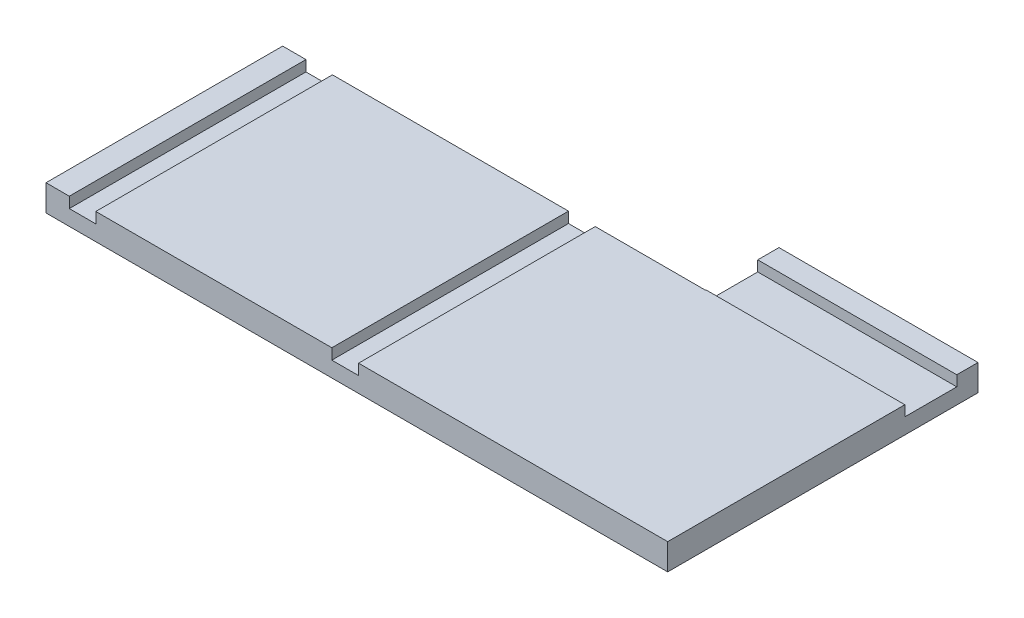
SolidWorks part; units mm, degrees
ref_plane "Front Plane" through (0, 0, 0) normal (0, 0, 1) x (1, 0, 0)
ref_plane "Top Plane" through (0, 0, 0) normal (0, 1, 0) x (1, 0, 0)
ref_plane "Right Plane" through (0, 0, 0) normal (1, 0, 0) x (0, 0, -1)
sketch "Sketch1" plane through (0, 0, 0) normal (0, 1, 0) x (1, 0, 0)
  line L0 (0, 45.1359) -> (5, 45.1359) construction
  line L1 (0, 0) -> (114.1267, 0)
  line L2 (0, 0) -> (0, 45.1359)
  line L3 (0, 45.1359) -> (76.1657, 45.1359)
  line L4 (114.1267, 0) -> (114.1267, 45.1359)
  line L5 (76.1657, 55.1359) -> (76.1657, 45.1359) construction
  line L7 (114.1267, 45.1359) -> (114.1267, 59.1839)
  line L8 (114.1267, 59.1839) -> (76.1657, 59.1839)
  line L9 (76.1657, 45.1359) -> (76.1657, 59.1839)
extrude "Boss-Extrude1" add sketch "Sketch1" along normal blind 5
sketch "Sketch2" plane through (0, 0, 0) normal (0, 0, 1) x (1, 0, 0)
  line L1 (-0.05, 2.95) -> (5.05, 2.95)
  line L2 (-0.05, 2.95) -> (-0.05, 5)
  line L3 (-0.05, 5) -> (5.05, 5)
  line L4 (5.05, 2.95) -> (5.05, 5)
  line L5 (0, 5) -> (114.1267, 5) construction
  line L6 (55.12, 2.95) -> (50.12, 2.95) construction
  line L7 (50.07, 2.95) -> (55.17, 2.95)
  line L8 (50.07, 2.95) -> (50.07, 5)
  line L9 (50.07, 5) -> (55.17, 5)
  line L10 (55.17, 2.95) -> (55.17, 5)
  line L11 (50.12, 2.95) -> (50.12, 22.5552) construction
  line L12 (55.12, 2.95) -> (55.12, 22.5552) construction
  line L13 (0, 2.95) -> (5, 2.95) construction
  line L14 (0, 28.566) -> (0, 2.95) construction
  line L15 (5, 28.566) -> (5, 2.95) construction
  point P13 (0, 0)
  point P14 (0, 0)
  point P21 (0, 0)
  dimension "D1" = 0
  dimension "D2" = 2.05
  dimension "D3" = 0.05
  dimension "D4" = 0.05
  dimension "D5" = 0
  dimension "D6" = 0.05
  dimension "D7" = 0.05
extrude "Cut-Extrude1" cut sketch "Sketch2" against normal through all both and the other way through all
sketch "Sketch3" plane through (114.1267, 0, 0) normal (1, 0, 0) x (0, 0, -1)
  line L0 (0, 5) -> (59.1839, 5) construction
  line L1 (45.1359, 5) -> (55.1359, 5)
  line L2 (45.1359, 5) -> (45.1359, 3)
  line L3 (45.1359, 3) -> (55.1359, 3)
  line L4 (55.1359, 5) -> (55.1359, 3)
  line L5 (55.1359, 28.5) -> (55.1359, 3) construction
  line L6 (45.1359, 28.5) -> (45.1359, 3) construction
  dimension "D1" = 2
extrude "Cut-Extrude2" cut sketch "Sketch3" against normal up to surface (66.5667 mm away)
sketch "Sketch4" plane through (0, 0, 0) normal (0, 0, 1) x (1, 0, 0)
  line L0 (5.05, 5) -> (50.07, 5) construction
  line L1 (0, 0) -> (-4.4446, 0)
  line L2 (0, 0) -> (0, 5)
  line L3 (0, 5) -> (-4.4446, 5)
  line L4 (-4.4446, 0) -> (-4.4446, 5)
extrude "Boss-Extrude2" add sketch "Sketch4" against normal up to surface (45.1359 mm away) up to face at (50.0971, 3.15, -45.1359)
sketch "Sketch5" plane through (114.1267, 0, 0) normal (1, 0, 0) x (0, 0, -1)
  line L0 (0, 5) -> (45.1359, 5) construction
  line L1 (45.1359, 3) -> (45.2359, 3)
  line L2 (45.1359, 3) -> (45.1359, 5)
  line L3 (45.1359, 5) -> (45.2359, 5)
  line L4 (45.2359, 3) -> (45.2359, 5)
  dimension "D1" = 0.1
extrude "Boss-Extrude3" add sketch "Sketch5" against normal up to surface (37.961 mm away) up to face at (76.1657, 2.6667, -53.1519)
